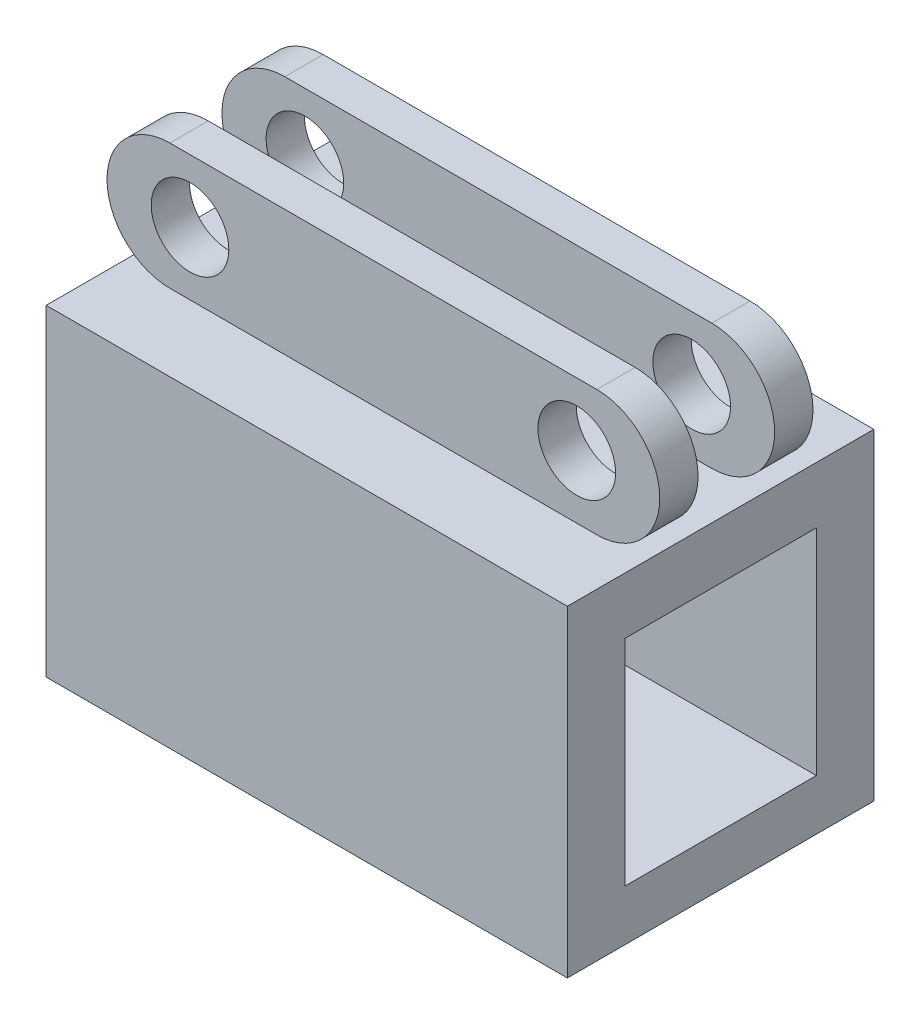
SolidWorks part; units mm, degrees
ref_plane "Front Plane" through (0, 0, 0) normal (0, 0, 1) x (1, 0, 0)
ref_plane "Top Plane" through (0, 0, 0) normal (0, 1, 0) x (1, 0, 0)
ref_plane "Right Plane" through (0, 0, 0) normal (1, 0, 0) x (0, 0, -1)
sketch "Sketch1" plane through (0, 0, 0) normal (0, 0, 1) x (1, 0, 0)
  line L0 (-27.86, 0) -> (27.86, 0) construction
  line L1 (-27.86, 8.2112) -> (27.86, 8.2112)
  line L2 (-27.86, -8.2112) -> (27.86, -8.2112)
  arc A0 (-27.86, 8.2112) -> (-27.86, -8.2112) centre (-27.86, 0) ccw
  arc A1 (27.86, -8.2112) -> (27.86, 8.2112) centre (27.86, 0) ccw
  point P3 (0, 0)
extrude "Boss-Extrude1" add sketch "Sketch1" along normal mid plane 20
sketch "Sketch3" plane through (0, 0, 0) normal (0, 0, 1) x (1, 0, 0)
  line L0 (-27.86, -8.2112) -> (27.86, -8.2112) construction
  line L1 (34.0134, -8.2112) -> (-34.0134, -8.2112)
  line L2 (34.0134, -8.2112) -> (34.0134, -50.2338)
  line L3 (34.0134, -50.2338) -> (-34.0134, -50.2338)
  line L4 (-34.0134, -8.2112) -> (-34.0134, -50.2338)
  line L5 (0, -8.2112) -> (0, 0) construction
extrude "Boss-Extrude2" add sketch "Sketch3" along normal mid plane 40
sketch "Sketch4" plane through (34.0134, 0, 0) normal (1, 0, 0) x (0, 0, -1)
  line L0 (0, -15.5986) -> (0, 0) construction
  line L1 (12.5, -15.5986) -> (-12.5, -15.5986)
  line L2 (12.5, -15.5986) -> (12.5, -43.5986)
  line L3 (12.5, -43.5986) -> (-12.5, -43.5986)
  line L4 (-12.5, -15.5986) -> (-12.5, -43.5986)
  dimension "D1" = 25
  dimension "D2" = 28
extrude "Cut-Extrude1" cut sketch "Sketch4" against normal through all
sketch "Sketch5" plane through (0, 0, 10) normal (0, 0, 1) x (1, 0, 0)
  line L0 (0, 0) -> (0, 37.5874) construction
  circle A0 centre (-25.241, 0) radius 5.0671
  circle A1 centre (25.241, 0) radius 5.0671
extrude "Cut-Extrude2" cut sketch "Sketch5" against normal through all
sketch "Sketch6" plane through (0, 0, 0) normal (0, 0, 1) x (1, 0, 0)
  line L1 (-82.5485, -8.2112) -> (84.0494, -8.2112)
  line L2 (-82.5485, -8.2112) -> (-82.5485, 34.7513)
  line L3 (-82.5485, 34.7513) -> (84.0494, 34.7513)
  line L4 (84.0494, -8.2112) -> (84.0494, 34.7513)
  line L5 (34.0134, -8.2112) -> (-34.0134, -8.2112) construction
extrude "Cut-Extrude3" cut sketch "Sketch6" against normal mid plane 10
